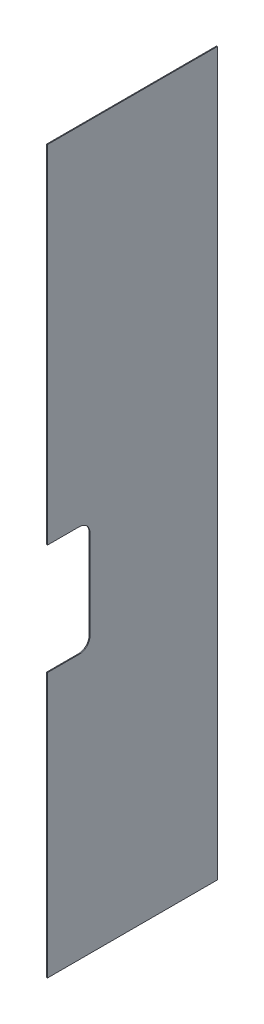
SolidWorks part; units mm, degrees
material "Delrin 2700 NC010, Low Viscosity Acetal Copolymer (SS)"
ref_plane "Front Plane" through (0, 0, 0) normal (0, 0, 1) x (1, 0, 0)
ref_plane "Top Plane" through (0, 0, 0) normal (0, 1, 0) x (1, 0, 0)
ref_plane "Right Plane" through (0, 0, 0) normal (1, 0, 0) x (0, 0, -1)
sketch "Sketch1" plane through (0, 0, 0) normal (1, 0, 0) x (0, 0, -1)
  line L0 (-222.25, 0) -> (-171.45, 0)
  line L1 (-165.1, 0) -> (165.1, 0) construction
  line L2 (-165.1, 0) -> (-165.1, -228.6) construction
  line L3 (-165.1, -228.6) -> (165.1, -228.6) construction
  line L4 (165.1, 0) -> (165.1, -228.6) construction
  line L5 (171.45, 0) -> (222.25, 0)
  line L6 (-171.45, 0) -> (-171.45, -215.9)
  line L7 (-152.4, -234.95) -> (152.4, -234.95)
  line L8 (171.45, 0) -> (171.45, -215.9)
  line L9 (-165.1, 0) -> (-165.1, 25.4) construction
  line L10 (-222.25, 0) -> (-222.25, -266.7)
  line L11 (-203.2, -285.75) -> (203.2, -285.75)
  line L12 (222.25, 0) -> (222.25, -266.7)
  line L13 (-165.1, 25.4) -> (165.1, 25.4) construction
  line L14 (165.1, 25.4) -> (165.1, 0) construction
  line L15 (0, -234.95) -> (0, -285.75)
  arc A0 (203.2, -285.75) -> (222.25, -266.7) centre (203.2, -266.7) ccw
  arc A1 (-203.2, -285.75) -> (-222.25, -266.7) centre (-203.2, -266.7) cw
  arc A2 (171.45, -215.9) -> (152.4, -234.95) centre (152.4, -215.9) cw
  arc A3 (-152.4, -234.95) -> (-171.45, -215.9) centre (-152.4, -215.9) cw
  dimension "D8" = 19.05
  dimension "D1" = 50.8
  dimension "D2" = 330.2
  dimension "D3" = 228.6
  dimension "D4" = 6.35
  dimension "D5" = 6.35
  dimension "D6" = 6.35
  dimension "D7" = 50.8
  dimension "D9" = 254
  dimension "D10" = 25.4
  dimension "D11" = 285.75
extrude "Boss-Extrude2" add sketch "Sketch1" along normal blind 0.254 contours L8 A2 L7 L15 L11 A0 L12 L5
sketch "Sketch11" plane through (0, 0, 0) normal (-1, 0, 0) x (0, 0, 1)
  line L0 (-171.45, 0) -> (-171.45, -215.9) construction
  line L1 (-171.45, -103.759) -> (-180.975, -103.759)
  line L2 (-171.45, -103.759) -> (-171.45, -136.779)
  line L3 (-171.45, -136.779) -> (-180.975, -136.779)
  line L4 (-184.15, -106.934) -> (-184.15, -133.604)
  line L5 (0, 0) -> (0, -234.95) construction
  line L6 (-171.45, -120.269) -> (-171.45, 0) construction
  line L7 (0, -234.95) -> (-152.4, -234.95) construction
  line L8 (-44.45, -234.95) -> (-31.75, -234.95)
  line L9 (-44.45, -234.95) -> (-44.45, -244.475)
  line L10 (-41.275, -247.65) -> (-34.925, -247.65)
  line L11 (-31.75, -234.95) -> (-31.75, -244.475)
  line L13 (-38.1, -234.95) -> (0, -234.95) construction
  arc A0 (-180.975, -136.779) -> (-184.15, -133.604) centre (-180.975, -133.604) cw
  arc A1 (-184.15, -106.934) -> (-180.975, -103.759) centre (-180.975, -106.934) cw
  arc A2 (-34.925, -247.65) -> (-31.75, -244.475) centre (-34.925, -244.475) ccw
  arc A3 (-41.275, -247.65) -> (-44.45, -244.475) centre (-41.275, -244.475) cw
  point P10 (-184.15, -136.779)
  point P13 (-184.15, -103.759)
  point P25 (-31.75, -247.65)
  point P28 (-44.45, -247.65)
  dimension "D4" = 3.175
  dimension "D8" = 3.175
  dimension "D1" = 12.7
  dimension "D2" = 33.02
  dimension "D3" = 120.269
  dimension "D5" = 12.7
  dimension "D6" = 12.7
  dimension "D7" = 38.1
extrude "Cut-Extrude1" cut sketch "Sketch11" against normal through all
sketch "Sketch13" plane through (0, 0, 0) normal (-1, 0, 0) x (0, 0, 1)
  line L1 (-222.25, 0) -> (-222.25, -266.7) construction
  line L2 (0, -285.75) -> (-222.25, -285.75)
  line L3 (0, -285.75) -> (0, -215.9)
  line L4 (0, -215.9) -> (-222.25, -215.9)
  line L6 (-222.25, -285.75) -> (-222.25, -215.9)
  dimension "D1" = 69.85
extrude "Cut-Extrude3" cut sketch "Sketch13" against normal through all
